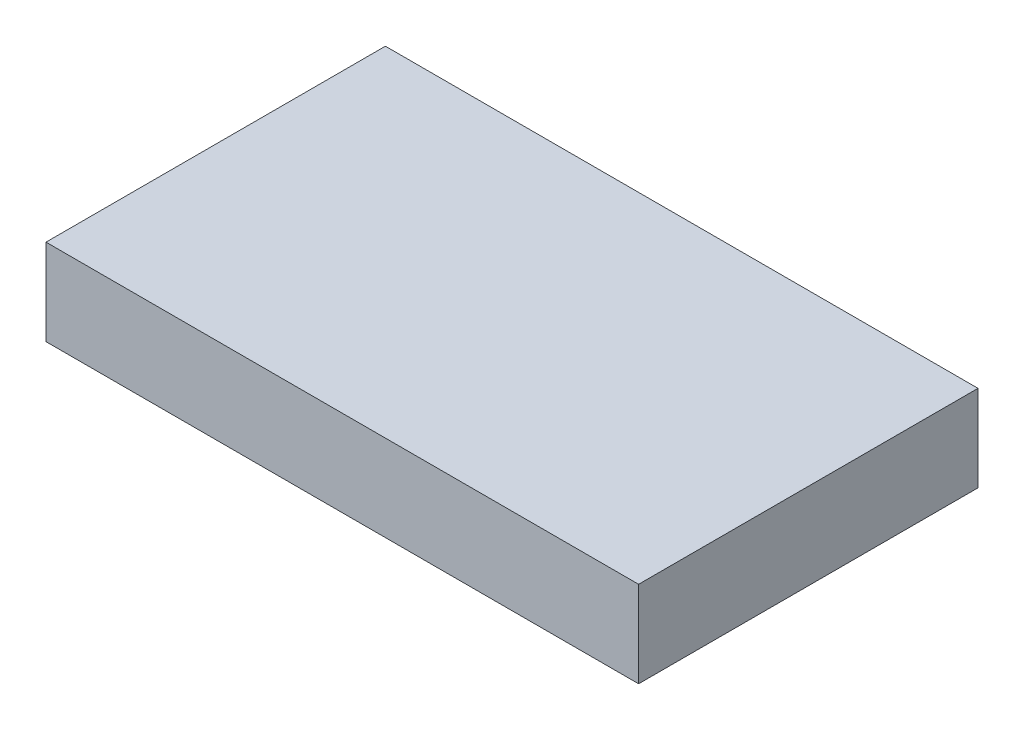
SolidWorks part; units mm, degrees
material "1060 Alloy"
ref_plane "Front Plane" through (0, 0, 0) normal (0, 0, 1) x (1, 0, 0)
ref_plane "Top Plane" through (0, 0, 0) normal (0, 1, 0) x (1, 0, 0)
ref_plane "Right Plane" through (0, 0, 0) normal (1, 0, 0) x (0, 0, -1)
sketch "Sketch1" plane through (0, 0, 0) normal (1, 0, 0) x (0, 0, -1)
  line L1 (-9.45, 0) -> (9.45, 0)
  line L2 (-9.45, 0) -> (-9.45, 4.8)
  line L3 (-9.45, 4.8) -> (9.45, 4.8)
  line L4 (9.45, 0) -> (9.45, 4.8)
  dimension "D1" = 18.9
  dimension "D2" = 4.8
extrude "Boss-Extrude1" add sketch "Sketch1" along normal blind 33
